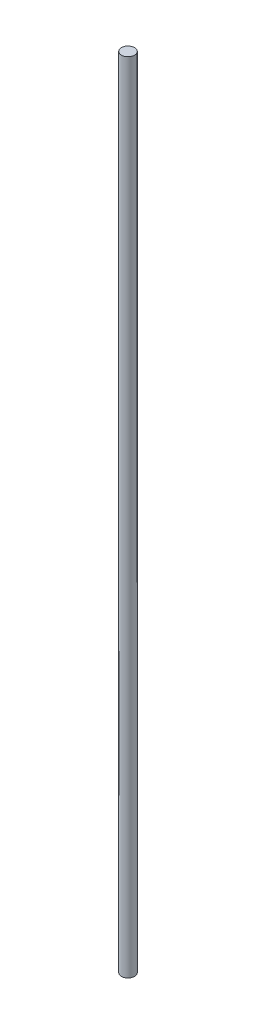
SolidWorks part; units mm, degrees
ref_plane "Спереди" through (0, 0, 0) normal (0, 0, 1) x (1, 0, 0)
ref_plane "Сверху" through (0, 0, 0) normal (0, 1, 0) x (1, 0, 0)
ref_plane "Справа" through (0, 0, 0) normal (1, 0, 0) x (0, 0, -1)
sketch "Эскиз1" plane through (0, 0, 0) normal (0, 1, 0) x (1, 0, 0)
  circle A0 centre (0, 0) radius 5
extrude "Бобышка-Вытянуть1" add sketch "Эскиз1" along normal blind 608
